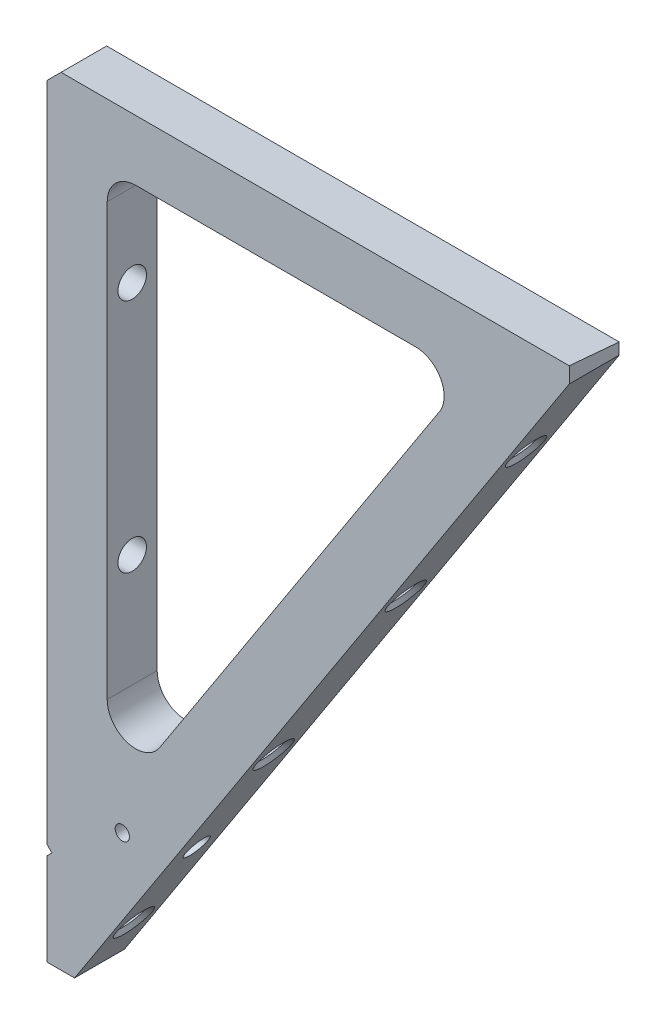
SolidWorks part; units mm, degrees
material "6061-T6 Al"
ref_plane "Front" through (0, 0, 0) normal (0, 0, 1) x (1, 0, 0)
ref_plane "Top" through (0, 0, 0) normal (0, 1, 0) x (1, 0, 0)
ref_plane "Right" through (0, 0, 0) normal (1, 0, 0) x (0, 0, -1)
sketch "Sketch1" plane through (0, 0, 0) normal (0, 0, 1) x (1, 0, 0)
  line L0 (0, 0) -> (0, -182.6405)
  line L1 (118.6082, 0) -> (0, -182.6405)
  line L2 (0, 0) -> (118.6082, 0)
  line L3 (13.4522, -13.462) -> (13.4522, -137.2088) construction
  line L4 (93.8142, -13.462) -> (13.4522, -137.2088) construction
  line L5 (19.8022, -13.462) -> (82.119, -13.462)
  line L6 (87.4445, -23.2705) -> (25.1277, -119.23)
  line L7 (13.4522, -19.812) -> (13.4522, -115.7715)
  line L8 (55, 0) -> (-55, 0) construction
  line L10 (13.4522, -13.462) -> (93.8142, -13.462) construction
  line L11 (-0.0098, 0) -> (-0.0098, -182.6557) construction
  line L12 (0, -55) -> (0, 55) construction
  line L13 (118.6082, 0) -> (-0.0098, -182.6557) construction
  line L14 (-0.0098, 0) -> (118.6082, 0) construction
  line L15 (19.8022, -19.812) -> (19.8022, -115.7715) construction
  arc A0 (13.4522, -115.7715) -> (25.1277, -119.23) centre (19.8022, -115.7715) ccw
  arc A1 (13.4522, -19.812) -> (19.8022, -13.462) centre (19.8022, -19.812) cw
  arc A2 (82.119, -13.462) -> (87.4445, -23.2705) centre (82.119, -19.812) cw
other "AlignGroup4" parameters "D4"=6.35, "D1"=3.6339, "D2"=18.9878, "D3"=11.6137, "D5"=217.7739, "D6"=19.8022, "D7"=82.119
extrude "Boss-Extrude1" add sketch "Sketch1" along normal blind 11.1252
hole_wizard "1/4-20 Tapped Hole1" positions "Sketch4" profile "Sketch3" tap size "1/4-20" standard "ANSI Inch"
sketch "Sketch4" plane through (0, -0.7781, 4.022) normal (-1, 0, 0) x (0, 0, 1)
  line L0 (1.5406, -37.4278) -> (1.5406, 0.7781) construction
  line L2 (1.5406, -37.4278) -> (1.5406, -89.8971) construction
  line L3 (1.5406, -89.8971) -> (1.5406, -139.0278) construction
  line L8 (7.1032, -181.8625) -> (-4.022, -181.8625) construction
  line L9 (7.1032, 0.7781) -> (-4.022, 0.7781) construction
  point P0 (1.5406, -139.0278)
  point P1 (1.5406, -37.4278)
  point P3 (1.5406, -89.8971)
other "AlignGroup5" parameters "D1"=0, "D2"=38.2059, "D3"=90.6752, "D4"=139.8059
sketch "Sketch3" plane through (0, -139.8059, 5.5626) normal (0, 1, 0) x (0, 0, 1)
  line L0 (0, 0) -> (0, 32.217)
  line L1 (0, 32.217) -> (2.5527, 30.6832)
  line L2 (2.5527, 30.6832) -> (2.5527, 15.24)
  line L3 (2.5527, 15.24) -> (3.175, 15.24)
  line L5 (3.175, 15.24) -> (3.175, 0.889)
  line L6 (3.175, 0.889) -> (4.064, 0)
  line L7 (4.064, 0) -> (0, 0)
  line L8 (-3.175, 0.889) -> (-4.064, 0) construction
  line L10 (0, 32.217) -> (-2.5527, 30.6832) construction
  line L11 (0, -6.35) -> (0, 107.95) construction
  dimension "Tap Drill Dia." = 5.1054
  dimension "Tap Drill Depth" = 30.6832
  dimension "Thread Major Dia." = 6.35
  dimension "Thread Depth" = 15.24
  dimension "Near C'Sink Dia." = 8.128
  dimension "Near C'Sink Angle" = 90
  dimension "Drill Angle" = 118
hole_wizard "1/4-20 Tapped Hole2" positions "Sketch7" profile "Sketch6" tap size "1/4-20" standard "ANSI Inch"
sketch "Sketch7" plane through (83.4252, -54.177, 0) normal (0.8387, -0.5446, 0) x (0, 0, -1)
  line L0 (-5.5626, 64.5986) -> (-5.5626, 32.5368) construction
  line L1 (-11.1252, 64.5986) -> (0, 64.5986) construction
  line L2 (-5.5626, 32.5368) -> (-5.5626, -16.663) construction
  line L3 (-5.5626, -16.663) -> (-5.5626, -70.638) construction
  line L4 (-5.5626, -70.638) -> (-5.5626, -127.788) construction
  line L10 (-11.1252, -153.1752) -> (0, -153.1752) construction
  point P26 (-5.5626, -16.663)
  point P28 (-5.5626, -70.638)
  point P30 (-5.5626, -127.788)
  point P42 (-5.5626, 32.5368)
other "AlignGroup6" parameters "D1"=0, "D2"=25.4, "D3"=82.55, "D4"=136.525, "D5"=185.7248
sketch "Sketch6" plane through (74.3499, -68.1517, 5.5626) normal (0, 0, 1) x (0.5446, 0.8387, 0)
  line L0 (0, 0) -> (0, 19.517)
  line L1 (0, 19.517) -> (2.5527, 17.9832)
  line L2 (2.5527, 17.9832) -> (2.5527, 15.24)
  line L3 (2.5527, 15.24) -> (3.175, 15.24)
  line L5 (3.175, 15.24) -> (3.175, 0.889)
  line L6 (3.175, 0.889) -> (4.064, 0)
  line L7 (4.064, 0) -> (0, 0)
  line L8 (-3.175, 0.889) -> (-4.064, 0) construction
  line L10 (0, 19.517) -> (-2.5527, 17.9832) construction
  line L11 (0, -6.35) -> (0, 107.95) construction
  dimension "Tap Drill Dia." = 5.1054
  dimension "Tap Drill Depth" = 17.9832
  dimension "Thread Major Dia." = 6.35
  dimension "Thread Depth" = 15.24
  dimension "Near C'Sink Dia." = 8.128
  dimension "Near C'Sink Angle" = 90
  dimension "Drill Angle" = 118
sketch "Sketch8" plane through (0, 0, 11.1252) normal (0, 0, 1) x (1, 0, 0)
  line L0 (0, -182.6405) -> (0, -173.1155)
  line L2 (0, -173.1155) -> (6.1856, -173.1155)
  line L3 (0, -182.6405) -> (118.6082, 0) construction
  line L4 (6.1856, -173.1155) -> (0, -182.6405)
  line L5 (0, -182.6405) -> (118.6082, 0) construction
  line L6 (0, 0) -> (0, -182.6405) construction
  dimension "D1" = 9.525
extrude "Cut-Extrude1" cut sketch "Sketch8" against normal through all
chamfer "Chamfer3" distance 3.175 angle 45 1 edges at (0, 0, 5.5626)
sketch "Sketch9" plane through (0, 0, 0) normal (-1, 0, 0) x (0, 0, 1)
  line L0 (11.1252, 0) -> (0, 0)
  line L1 (11.1252, 0) -> (0, -0.9733)
  line L2 (0, -0.9733) -> (0, 0)
  dimension "D1" = 5
extrude "Cut-Extrude2" cut sketch "Sketch9" against normal through all
sketch "Sketch10" plane through (0, 0, 11.1252) normal (0, 0, 1) x (1, 0, 0)
  line L0 (118.6082, 0) -> (116.3222, 0)
  line L1 (118.6082, 0) -> (3.175, 0) construction
  line L2 (116.3222, 0) -> (116.3222, -3.5201)
  line L3 (6.1856, -173.1155) -> (118.6082, 0) construction
  line L4 (118.6082, 0) -> (116.3222, -3.5201)
  dimension "D1" = 2.286
extrude "Cut-Extrude3" cut sketch "Sketch10" against normal through all
hole_wizard "1/8 (0.125) Diameter Hole1" positions "Sketch12" profile "Sketch13" hole size "1/8" standard "ANSI Inch" end condition through all
sketch "Sketch12" plane through (0, 0, 11.1252) normal (0, 0, 1) x (1, 0, 0)
  line L3 (15.24, -139.8059) -> (16.8148, -139.8059) construction
  line L4 (15.24, -136.6309) -> (15.24, -142.9809) construction
  point P0 (16.8148, -139.8059)
  dimension "D2" = 1.5748
sketch "Sketch13" plane through (16.8148, -139.8059, 11.1252) normal (1, 0, 0) x (0, -1, 0)
  line L0 (0, 0) -> (0, 11.1252)
  line L1 (0, 11.1252) -> (1.5875, 11.1252)
  line L2 (1.5875, 11.1252) -> (1.5875, 0)
  line L5 (1.5875, 0) -> (0, 0)
  line L11 (0, -6.35) -> (0, 107.95) construction
  dimension "Thru Hole Dia." = 3.175
  dimension "Thru Hole Depth" = 11.1252
sketch "Sketch14" plane through (0, 0, 11.1252) normal (0, 0, 1) x (1, 0, 0)
  line L0 (0, -150.3825) -> (0, -152.6685)
  line L1 (0, -3.175) -> (0, -173.1155) construction
  line L2 (0, -150.3825) -> (1.143, -151.5255)
  line L3 (0, -152.6685) -> (1.143, -151.5255)
  line L4 (6.1856, -173.1155) -> (0, -173.1155) construction
  dimension "D1" = 45
  dimension "D2" = 45
  dimension "D3" = 2.286
  dimension "D4" = 21.59
extrude "Cut-Extrude4" cut sketch "Sketch14" against normal through all
